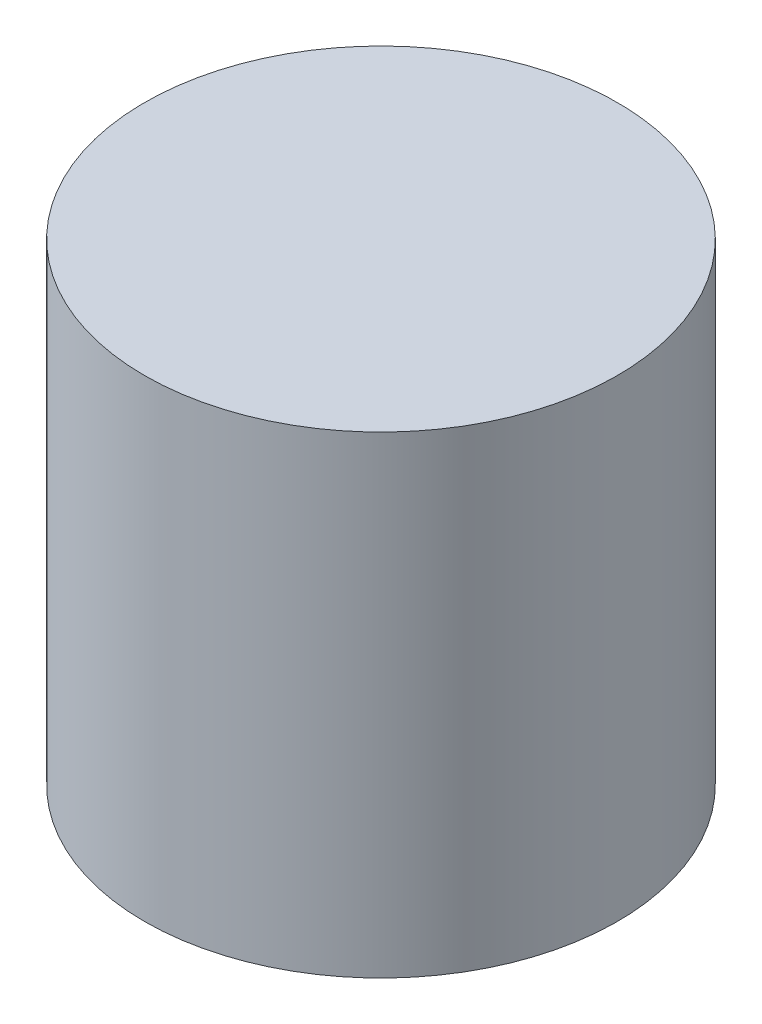
SolidWorks part; units mm, degrees
ref_plane "Front Plane" through (0, 0, 0) normal (0, 0, 1) x (1, 0, 0)
ref_plane "Top Plane" through (0, 0, 0) normal (0, 1, 0) x (1, 0, 0)
ref_plane "Right Plane" through (0, 0, 0) normal (1, 0, 0) x (0, 0, -1)
sketch "Sketch1" plane through (0, 0, 0) normal (0, 1, 0) x (1, 0, 0)
  circle A0 centre (0, 0) radius 3.175
  dimension "D1" = 6.35
extrude "Boss-Extrude1" add sketch "Sketch1" along normal blind 6.35
